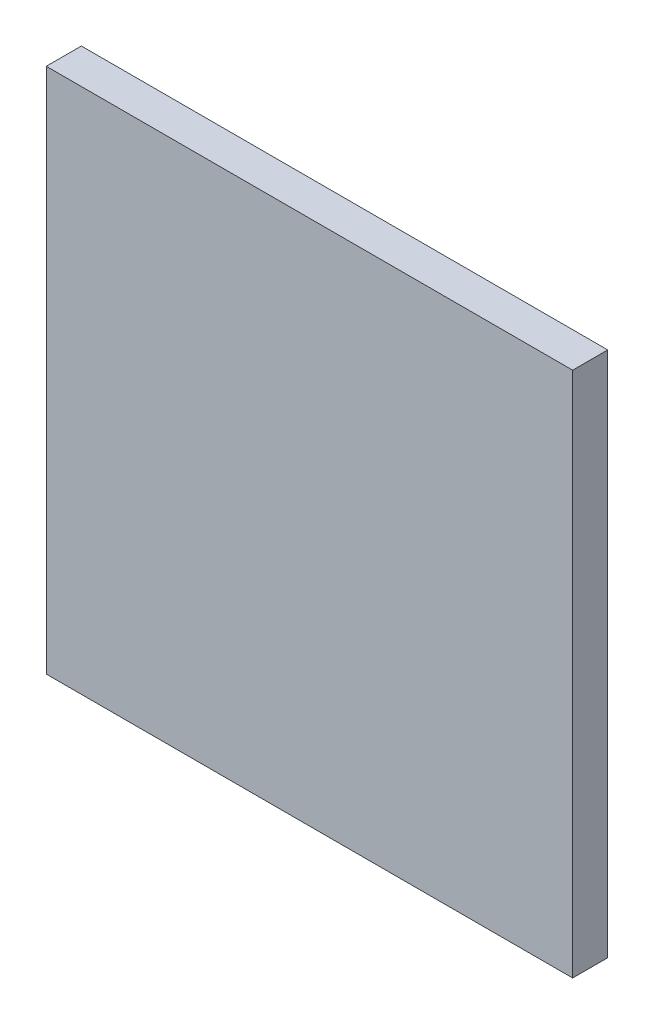
SolidWorks part; units mm, degrees
ref_plane "Front Plane" through (0, 0, 0) normal (0, 0, 1) x (1, 0, 0)
ref_plane "Top Plane" through (0, 0, 0) normal (0, 1, 0) x (1, 0, 0)
ref_plane "Right Plane" through (0, 0, 0) normal (1, 0, 0) x (0, 0, -1)
sketch "Sketch1" plane through (0, 0, 0) normal (0, 0, 1) x (1, 0, 0)
  line L0 (-7.5, 7.5) -> (7.5, 7.5)
  line L1 (7.5, 7.5) -> (7.5, -7.5)
  line L2 (7.5, -7.5) -> (-7.5, -7.5)
  line L3 (-7.5, -7.5) -> (-7.5, 7.5)
extrude "Component_Outline" add sketch "Sketch1" along normal blind 1 separate body
sketch3d "3DSketch1"
  line L0 (0, 0, 0) -> (1, 0, 0)
  line L1 (0, 0, 0) -> (0, 1, 0)
  line L2 (0, 0, 0) -> (0, 0, 1)
  point P0 (0, 0, 0)
